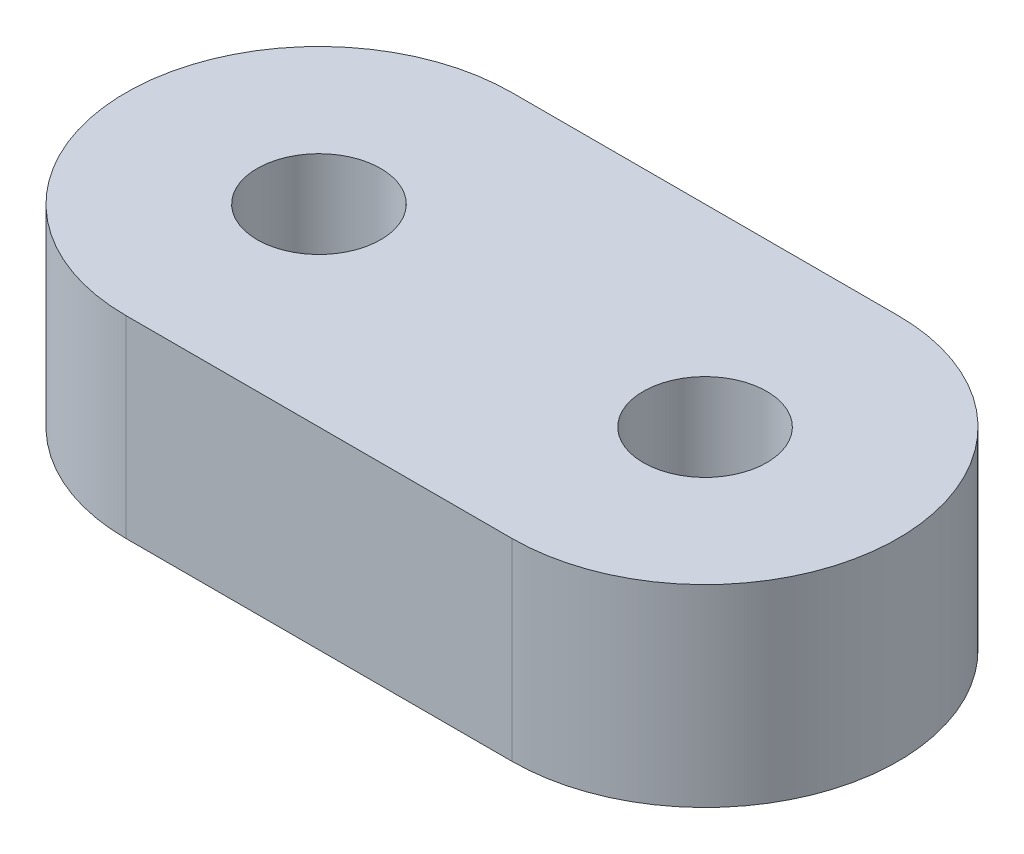
SolidWorks part; units mm, degrees
material "3D_printed_PLA"
ref_plane "Front Plane" through (0, 0, 0) normal (0, 0, 1) x (1, 0, 0)
ref_plane "Top Plane" through (0, 0, 0) normal (0, 1, 0) x (1, 0, 0)
ref_plane "Right Plane" through (0, 0, 0) normal (1, 0, 0) x (0, 0, -1)
sketch "Sketch1" plane through (0, 0, 0) normal (0, 1, 0) x (1, 0, 0)
  line L0 (5, 0) -> (-5, 0) construction
  line L1 (5, -5) -> (-5, -5)
  line L2 (5, 5) -> (-5, 5)
  arc A0 (5, -5) -> (5, 5) centre (5, 0) ccw
  arc A1 (-5, 5) -> (-5, -5) centre (-5, 0) ccw
  circle A2 centre (-5, 0) radius 1.6
  circle A3 centre (5, 0) radius 1.6
  point P2 (0, 0)
  dimension "D2" = 3.2
  dimension "D3" = 5
  dimension "D1" = 10
extrude "Boss-Extrude1" add sketch "Sketch1" along normal mid plane 5
